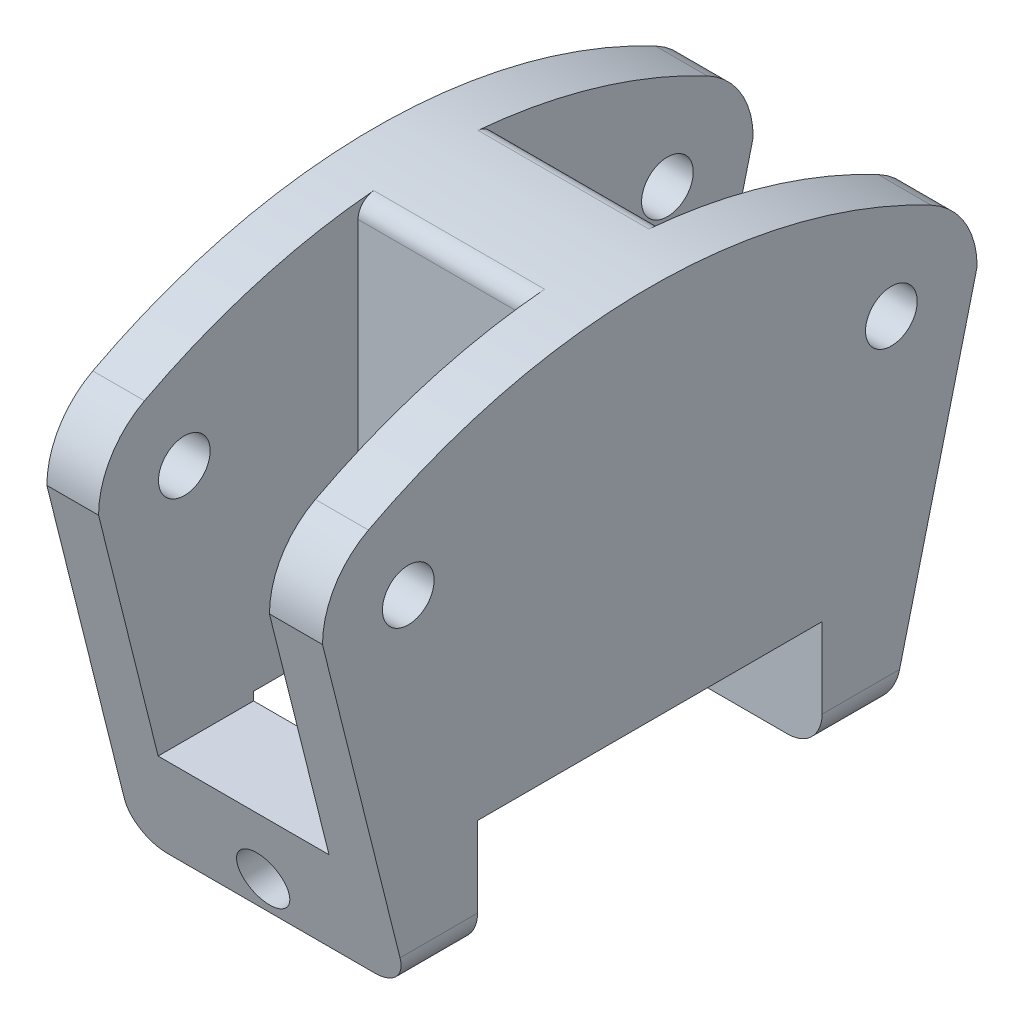
SolidWorks part; units mm, degrees
ref_plane "Front Plane" through (0, 0, 0) normal (0, 0, 1) x (1, 0, 0)
ref_plane "Top Plane" through (0, 0, 0) normal (0, 1, 0) x (1, 0, 0)
ref_plane "Right Plane" through (0, 0, 0) normal (1, 0, 0) x (0, 0, -1)
sketch "Sketch3" plane through (0, 0, 0) normal (1, 0, 0) x (0, 0, -1)
  line L0 (-14, 0) -> (14, 0)
  line L1 (14, 0) -> (19, 20)
  line L2 (-19, 20) -> (19, 20) construction
  line L3 (-14, 0) -> (-19, 20)
  line L4 (-19, 20) -> (-19, 43.2343) construction
  line L5 (19, 20) -> (19, 39.4685) construction
  arc A0 (-19, 20) -> (-16.3333, 24.4222) centre (-14, 20) cw
  arc A1 (19, 20) -> (16.3333, 24.4222) centre (14, 20) ccw
  arc A2 (-16.3333, 24.4222) -> (16.3333, 24.4222) centre (0, -6.533) cw
  point P3 (0, 0)
  dimension "D4" = 35
  dimension "D5" = 5
  dimension "D1" = 28
  dimension "D2" = 20
  dimension "D3" = 38
extrude "Boss-Extrude1" add sketch "Sketch3" along normal blind 16
sketch "Sketch4" plane through (16, 0, 0) normal (1, 0, 0) x (0, 0, -1)
  line L0 (-10, 0) -> (-10, 6.652)
  line L1 (-10, 0) -> (10, 0)
  line L2 (-10, 6.652) -> (10, 6.652)
  line L3 (10, 0) -> (10, 6.652)
  line L4 (-14, 0) -> (14, 0) construction
  line L6 (-14, 0) -> (-10, 0) construction
  line L7 (10, 0) -> (14, 0) construction
  dimension "D2" = 10
  dimension "D3" = 10
extrude "Cut-Extrude1" cut sketch "Sketch4" against normal through all
sketch "Sketch5" plane through (0, 0, 0) normal (-1, 0, 0) x (0, 0, 1)
  line L0 (-10, 6.652) -> (-10, 29.9939) construction
  line L1 (-19, 20) -> (23.4481, 20) construction
  line L2 (10, 6.652) -> (10, 29.9939) construction
  circle A0 centre (-14.0211, 20) radius 1.5
  dimension "D1" = 3
extrude "Cut-Extrude2" cut sketch "Sketch5" against normal through all contours A0
mirror "Mirror3" about plane through (0, 0, 0) normal (0, 0, 1) of "Cut-Extrude2"
ref_plane "Plane1" through (0, 29.1647, 0) normal (0, 1, 0) x (1, 0, 0)
sketch "Sketch6" plane through (0, 29.1647, 0) normal (0, 1, 0) x (1, 0, 0)
  line L0 (7.9603, -20.9394) -> (7.9603, 24.8882) construction
  line L1 (12.92, 3.9384) -> (3.0006, 3.9384)
  line L2 (12.92, 3.9384) -> (12.92, 22.9444)
  line L3 (12.92, 22.9444) -> (3.0006, 22.9444)
  line L4 (3.0006, 22.9444) -> (3.0006, 3.9384)
  line L7 (16, 6.0929) -> (16, 35.0754) construction
  line L8 (16, -16.3333) -> (16, 16.3333) construction
  line L9 (0, 5.1597) -> (0, 35.9536) construction
  line L10 (0, 16.3333) -> (0, -16.3333) construction
  point P5 (7.9603, 3.9384)
  dimension "D1" = 4.9597
  dimension "D2" = 19.006
  dimension "D3" = 3.08
  dimension "D4" = 3.0006
  dimension "D5" = 4.9597
extrude "Cut-Extrude3" cut sketch "Sketch6" against normal blind 23
mirror "Mirror4" about plane through (0, 0, 0) normal (0, 0, 1) of "Cut-Extrude3"
fillet "Fillet3" radius 2 2 edges at (7.9603, 6.652, 3.9384) (7.9603, 6.652, -3.9384)
fillet "Fillet6" radius 1 2 edges at (7.9603, 28.2447, 3.9384) (7.9603, 28.2447, -3.9384)
ref_plane "Plane2" through (0, 0, 20.7726) normal (0, 0, 1) x (1, 0, 0)
sketch "Sketch7" plane through (0, 0, 20.7726) normal (0, 0, 1) x (1, 0, 0)
  line L0 (8.0566, -2.1027) -> (8.0566, 29.8123) construction
  line L1 (1.6625, 0) -> (26.2389, 0) construction
  line L2 (16, 0) -> (0, 0) construction
  circle A0 centre (8.0566, 2) radius 1.5
  dimension "D1" = 3
  dimension "D2" = 2
extrude "Cut-Extrude4" cut sketch "Sketch7" against normal through all
fillet "Fillet7" radius 2 4 edges at (0, 0, -12) (0, 0, 12) (16, 0, 12) (16, 0, -12)
